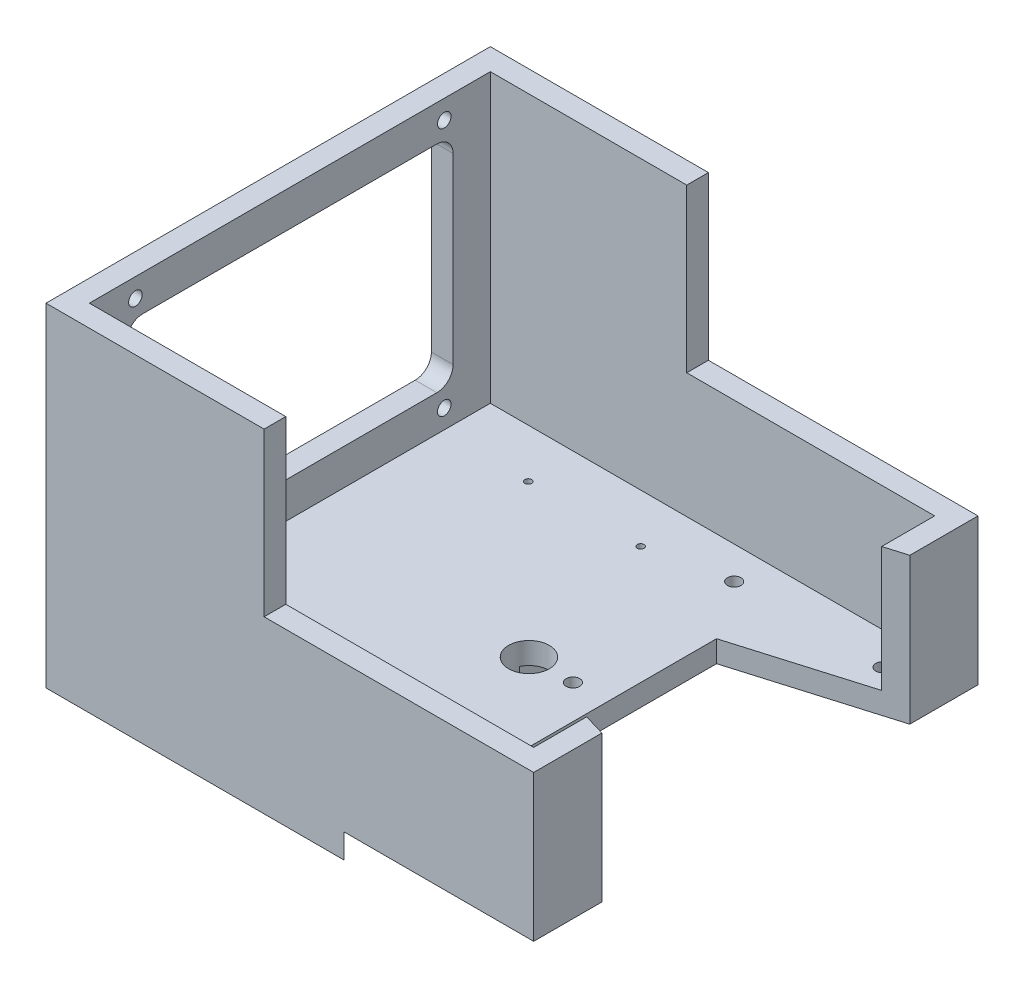
SolidWorks part; units mm, degrees
ref_plane "Front Plane" through (0, 0, 0) normal (0, 0, 1) x (1, 0, 0)
ref_plane "Top Plane" through (0, 0, 0) normal (0, 1, 0) x (1, 0, 0)
ref_plane "Right Plane" through (0, 0, 0) normal (1, 0, 0) x (0, 0, -1)
sketch "Sketch1" plane through (0, 0, 0) normal (0, 1, 0) x (1, 0, 0)
  line L0 (185, 85) -> (35, 40.5)
  line L1 (-90, 82) -> (90, 82)
  line L2 (-90, 82) -> (-90, -82)
  line L3 (-90, -82) -> (90, -82)
  line L4 (90, 82) -> (90, -82)
  line L5 (-90, 82) -> (90, -82) construction
  line L6 (-90, -82) -> (90, 82) construction
  line L8 (35, -40.5) -> (185, -85)
  line L9 (185, 85) -> (185, -85)
  line L10 (-90, 0) -> (90, 0) construction
  line L11 (35, 40.5) -> (35, -40.5)
  point P0 (0, 0)
  point P8 (185, 0)
  point P9 (35, 0)
  dimension "D1" = 164
  dimension "D2" = 180
  dimension "D3" = 85
  dimension "D4" = 81
  dimension "D5" = 85
  dimension "D6" = 55
  dimension "D7" = 150
extrude "Boss-Extrude1" add sketch "Sketch1" along normal blind 8
sketch "Sketch2" plane through (0, 0, 0) normal (0, -1, 0) x (1, 0, 0)
  line L0 (-90, -82) -> (90, -82) construction
  line L1 (90, 82) -> (20, 82)
  line L2 (90, 82) -> (90, -82)
  line L3 (90, -82) -> (20, -82)
  line L4 (-0.5, 61.5) -> (-0.5, -61.5)
  line L6 (-90, 82) -> (90, 82)
  line L7 (-90, 82) -> (-90, -82)
  line L8 (-90, -82) -> (90, -82)
  line L9 (90, 82) -> (90, -82)
  arc A0 (20, -82) -> (-0.5, -61.5) centre (20, -61.5) cw
  arc A1 (20, 82) -> (-0.5, 61.5) centre (20, 61.5) ccw
  point P11 (-0.5, -82)
  dimension "D2" = 20.5
  dimension "D1" = 90.5
extrude "Boss-Extrude2" add sketch "Sketch2" along normal blind 9
sketch "Sketch3" plane through (0, 8, 0) normal (0, 1, 0) x (1, 0, 0)
  line L0 (-90, 82) -> (-90, -82)
  line L1 (-90, -82) -> (90, -82)
  line L2 (90, -82) -> (90, -56.8167)
  line L3 (90, -56.8167) -> (35, -40.5)
  line L5 (35, 40.5) -> (90, 56.8167)
  line L6 (90, 56.8167) -> (90, 82)
  line L7 (90, 82) -> (-90, 82)
  line L17 (27, 46.4713) -> (82, 62.788)
  line L18 (35, 40.5) -> (35, -40.5)
  line L19 (82, 62.788) -> (82, 74)
  line L20 (82, 74) -> (-82, 74)
  line L21 (-82, 74) -> (-82, -74)
  line L22 (-82, -74) -> (82, -74)
  line L23 (82, -74) -> (82, -62.788)
  line L24 (82, -62.788) -> (27, -46.4713)
  line L25 (27, 46.4713) -> (27, -46.4713)
  line L26 (82, 62.788) -> (82, -62.788)
  dimension "D1" = 8
extrude "Boss-Extrude3" add sketch "Sketch3" along normal blind 106
sketch "Sketch4" plane through (0, 8, 0) normal (0, 1, 0) x (1, 0, 0)
  line L0 (90, 56.8167) -> (90, 82) construction
  line L1 (90, 82) -> (-90, 82) construction
  line L2 (-82, 0) -> (35, 0) construction
  line L3 (-82, 74) -> (-82, -74) construction
  line L4 (35, 40.5) -> (35, -40.5) construction
  line L5 (74.76, 62) -> (-82, 62) construction
  circle A0 centre (74.76, 62) radius 2.5
  circle A1 centre (6.25, 0) radius 7.5
  circle A3 centre (22.5, 0) radius 2.5
  circle A4 centre (20, 62) radius 2.5
  circle A5 centre (20, -62) radius 2.5
  circle A6 centre (74.76, -62) radius 2.5
  dimension "D2" = 5
  dimension "D5" = 15
  dimension "D7" = 5
  dimension "D1" = 15.24
  dimension "D3" = 20
  dimension "D4" = 28.75
  dimension "D6" = 16.25
  dimension "D8" = 54.76
extrude "Cut-Extrude1" cut sketch "Sketch4" against normal up to next
sketch "Sketch5" plane through (0, 8, 0) normal (0, 1, 0) x (1, 0, 0)
  line L0 (-82, 0) -> (35, 0) construction
  line L1 (-82, 74) -> (-82, -74) construction
  line L2 (35, 40.5) -> (35, -40.5) construction
  line L3 (-29.25, 60) -> (-29.25, 0) construction
  line L4 (-54, 60) -> (-4.5, 60)
  line L5 (-54, 60) -> (-54, -60)
  line L6 (-54, -60) -> (-4.5, -60)
  line L7 (-4.5, 60) -> (-4.5, -60)
  line L8 (-54, 60) -> (-4.5, -60) construction
  line L9 (-54, -60) -> (-4.5, 60) construction
  circle A0 centre (-50, 56) radius 1.25
  circle A1 centre (-8.5, 56) radius 1.25
  circle A2 centre (-8.5, -56) radius 1.25
  circle A3 centre (-50, -56) radius 1.25
  point P6 (-29.25, 0)
  point P11 (-54, 0)
  dimension "D6" = 2.5
  dimension "D1" = 49.5
  dimension "D2" = 120
  dimension "D3" = 28
  dimension "D4" = 4
  dimension "D5" = 4
extrude "Cut-Extrude2" cut sketch "Sketch5" against normal up to next contours A0 | A1 | A3 | A2
sketch "Sketch7" plane through (0, 0, 82) normal (0, 0, 1) x (1, 0, 0)
  line L1 (90, 114) -> (-9.5, 114)
  line L2 (90, 114) -> (90, 54)
  line L3 (90, 54) -> (-9.5, 54)
  line L4 (-9.5, 114) -> (-9.5, 54)
  dimension "D1" = 60
  dimension "D2" = 99.5
extrude "Cut-Extrude3" cut sketch "Sketch7" against normal through all
sketch "Sketch8" plane through (-82, 0, 0) normal (1, 0, 0) x (0, 0, -1)
  line L0 (0, 114) -> (0, 8) construction
  line L1 (74, 114) -> (-74, 114) construction
  line L2 (40.5, 8) -> (-40.5, 8) construction
  line L4 (-57, 107) -> (57, 107)
  line L5 (-57, 107) -> (-57, 15)
  line L6 (-57, 15) -> (57, 15)
  line L7 (57, 107) -> (57, 15)
  line L8 (-57, 107) -> (57, 15) construction
  line L9 (-57, 15) -> (57, 107) construction
  line L10 (-54.25, 100.75) -> (54.25, 100.75)
  line L11 (-60.25, 94.75) -> (-60.25, 27.25)
  line L12 (-54.25, 21.25) -> (54.25, 21.25)
  line L13 (60.25, 94.75) -> (60.25, 27.25)
  line L14 (-60.25, 100.75) -> (60.25, 21.25) construction
  line L15 (-60.25, 21.25) -> (60.25, 100.75) construction
  circle A0 centre (-57, 107) radius 2.5
  circle A1 centre (57, 107) radius 2.5
  circle A2 centre (-57, 15) radius 2.5
  circle A3 centre (57, 15) radius 2.5
  arc A4 (54.25, 21.25) -> (60.25, 27.25) centre (54.25, 27.25) ccw
  arc A5 (-60.25, 27.25) -> (-54.25, 21.25) centre (-54.25, 27.25) ccw
  arc A6 (54.25, 100.75) -> (60.25, 94.75) centre (54.25, 94.75) cw
  arc A7 (-54.25, 100.75) -> (-60.25, 94.75) centre (-54.25, 94.75) ccw
  point P6 (0, 61)
  point P15 (0, 61)
  dimension "D3" = 5
  dimension "D6" = 6
  dimension "D1" = 114
  dimension "D2" = 92
  dimension "D4" = 79.5
  dimension "D5" = 120.5
extrude "Cut-Extrude4" cut sketch "Sketch8" against normal up to next contours L4 A0 L5 | L5 A0 L4 | L4 A1 L7 | L7 A1 L4 | L5 A2 L6 | L6 A2 L5 | L7 A3 L6 | L6 A3 L7 | L11 A5 L12 A4 L13 A6 L10 A7
